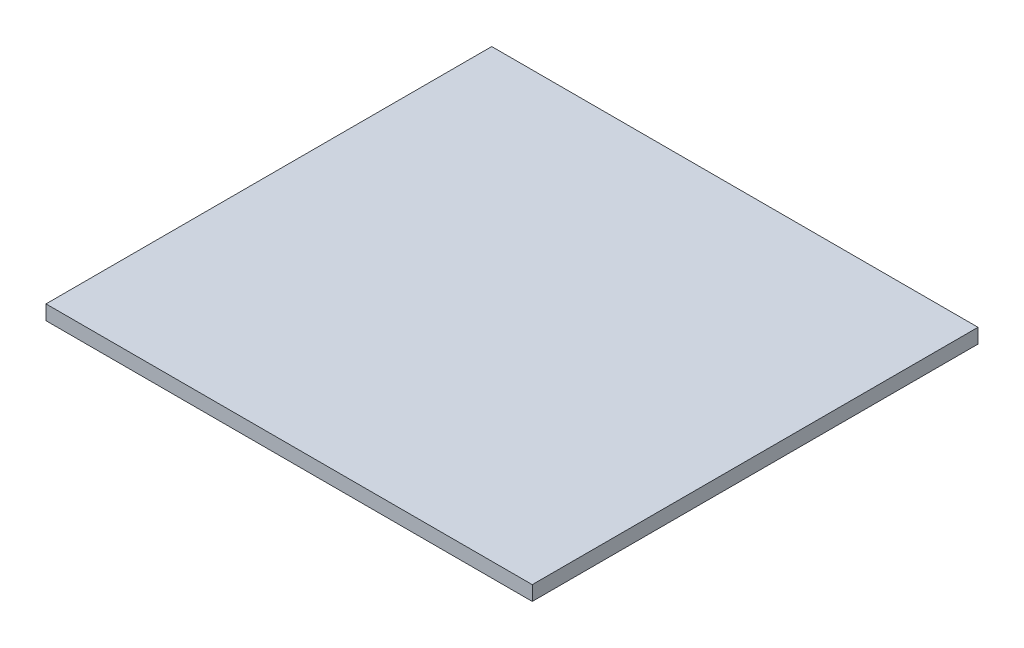
SolidWorks part; units mm, degrees
ref_plane "Спереди" through (0, 0, 0) normal (0, 0, 1) x (1, 0, 0)
ref_plane "Сверху" through (0, 0, 0) normal (0, 1, 0) x (1, 0, 0)
ref_plane "Справа" through (0, 0, 0) normal (1, 0, 0) x (0, 0, -1)
sketch "Эскиз1" plane through (0, 0, 0) normal (0, 1, 0) x (1, 0, 0)
  line L1 (300, -275) -> (-300, -275)
  line L2 (300, -275) -> (300, 275)
  line L3 (300, 275) -> (-300, 275)
  line L4 (-300, -275) -> (-300, 275)
  line L5 (300, -275) -> (-300, 275) construction
  line L6 (300, 275) -> (-300, -275) construction
  point P0 (0, 0)
  dimension "D1" = 600
  dimension "D2" = 550
extrude "Бобышка-Вытянуть1" add sketch "Эскиз1" along normal blind 18
